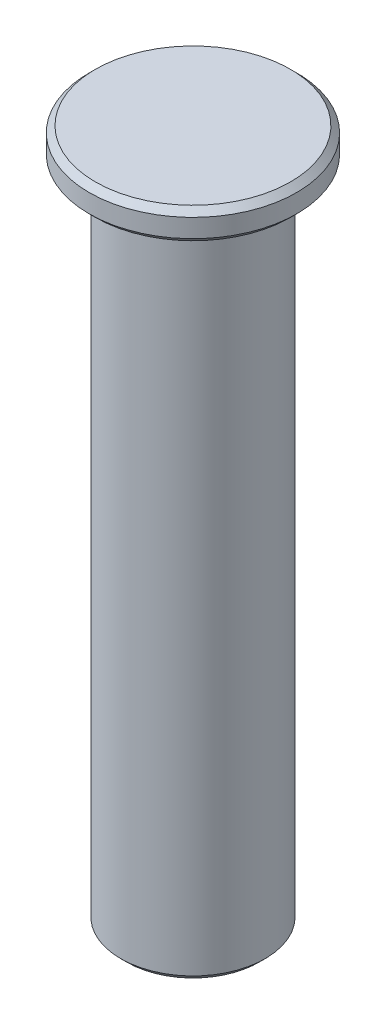
SolidWorks part; units mm, degrees
ref_plane "Front Plane" through (0, 0, 0) normal (0, 0, 1) x (1, 0, 0)
ref_plane "Top Plane" through (0, 0, 0) normal (0, 1, 0) x (1, 0, 0)
ref_plane "Right Plane" through (0, 0, 0) normal (1, 0, 0) x (0, 0, -1)
sketch "Sketch1" plane through (0, 0, 0) normal (0, 1, 0) x (1, 0, 0)
  circle A0 centre (0, 0) radius 4.7
  dimension "D1" = 9.4
extrude "Boss-Extrude1" add sketch "Sketch1" along normal blind 45
sketch "Sketch2" plane through (0, 45, 0) normal (0, 1, 0) x (1, 0, 0)
  circle A0 centre (0, 0) radius 6.75
  dimension "D1" = 13.5
extrude "Boss-Extrude2" add sketch "Sketch2" against normal blind 2
chamfer "Chamfer2" distance 0.4 angle 45 2 edges at (0, 43, 6.75) (0, 45, 6.75)
chamfer "Chamfer3" distance 0.4 angle 45 1 edges at (0, 0, 4.7)
